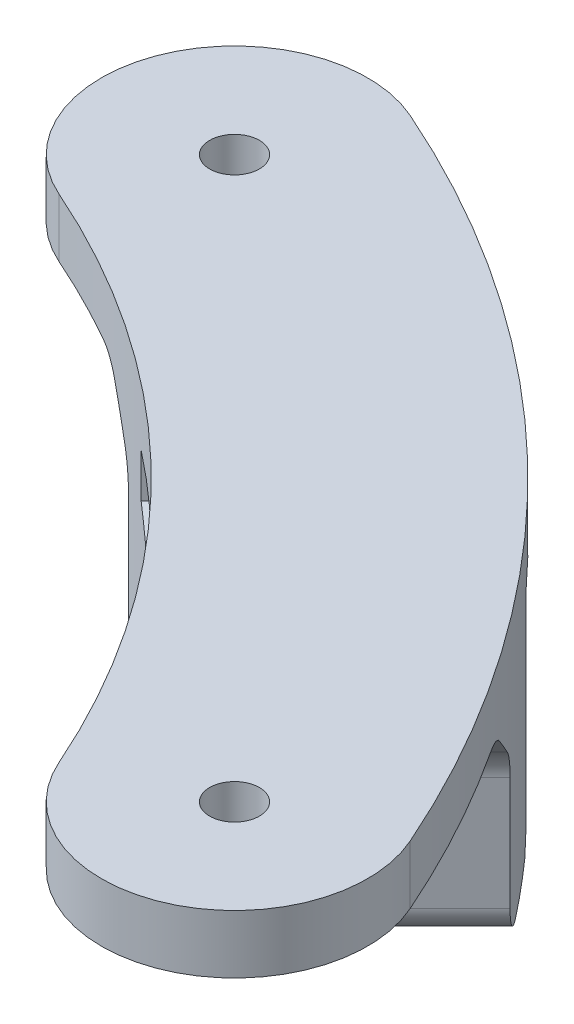
SolidWorks part; units mm, degrees
ref_plane "Front Plane" through (0, 0, 0) normal (0, 0, 1) x (1, 0, 0)
ref_plane "Top Plane" through (0, 0, 0) normal (0, 1, 0) x (1, 0, 0)
ref_plane "Right Plane" through (0, 0, 0) normal (1, 0, 0) x (0, 0, -1)
sketch "Sketch1" plane through (0, -74.9015, 0) normal (0, -1, 0) x (1, 0, 0)
  circle A0 centre (30.1717, -68.5087) radius 1.7
  circle A1 centre (68.5087, -30.1717) radius 1.7
  arc A2 (33.8428, -76.8444) -> (76.8444, -33.8428) centre (0, 0) ccw construction
  arc A3 (21.5669, -71.4952) -> (33.8428, -76.8444) centre (30.1717, -68.5087) ccw construction
  arc A4 (26.5006, -60.1729) -> (33.8428, -76.8444) centre (30.1717, -68.5087) ccw construction
  arc A5 (76.8444, -33.8428) -> (60.1729, -26.5006) centre (68.5087, -30.1717) ccw construction
  arc A6 (33.8428, -76.8444) -> (76.8444, -33.8428) centre (0, 0) ccw
  arc A7 (21.5669, -71.4952) -> (33.8428, -76.8444) centre (30.1717, -68.5087) ccw
  arc A8 (26.5006, -60.1729) -> (33.8428, -76.8444) centre (30.1717, -68.5087) ccw
  arc A9 (76.8444, -33.8428) -> (60.1729, -26.5006) centre (68.5087, -30.1717) ccw
  arc A10 (60.1729, -26.5006) -> (26.5006, -60.1729) centre (0, 0) cw
  arc M17 (21.5669, -71.4952) -> (33.8428, -76.8444) centre (30.1717, -68.5087) ccw
  arc M18 (33.8428, -76.8444) -> (76.8444, -33.8428) centre (0, 0) ccw
  arc M19 (76.8444, -33.8428) -> (71.4952, -21.5669) centre (68.5087, -30.1717) ccw
  circle M28 centre (68.5087, -30.1717) radius 1.7
  circle M29 centre (30.1717, -68.5087) radius 1.7
extrude "Boss-Extrude1" add sketch "Sketch1" along normal blind 4 contours A9 A10 A8 M17 M18 M19 M28 M29
ref_plane "Plane1" through (48.1381, 0, -48.1381) normal (0.7071, 0, -0.7071) x (-0.7071, 0, -0.7071)
ref_plane "Plane2" through (62.2802, 0, -62.2802) normal (0.7071, 0, -0.7071) x (-0.7071, 0, -0.7071)
sketch "Sketch2" plane through (62.2802, 0, -62.2802) normal (0.7071, 0, -0.7071) x (-0.7071, 0, -0.7071)
  line L0 (-12, -78.9015) -> (-12, -93.9015)
  line L1 (-30.4067, -78.9015) -> (30.4067, -78.9015) construction
  line L2 (-12, -93.9015) -> (-4, -93.9015)
  line L3 (-4, -93.9015) -> (-4, -78.9015)
  line L4 (-4, -78.9015) -> (-12, -78.9015)
  line L5 (0, -78.9015) -> (0, -94.9061) construction
  line L6 (4, -93.9015) -> (12, -93.9015)
  line L7 (12, -93.9015) -> (12, -78.9015)
  line L8 (12, -78.9015) -> (8, -78.9015)
  line L9 (8, -81.9015) -> (4, -84.2109)
  line L10 (4, -84.2109) -> (4, -93.9015)
  line L11 (8, -78.9015) -> (8, -81.9015)
  dimension "D1" = 8
  dimension "D2" = 15
  dimension "D3" = 8
  dimension "D4" = 3
  dimension "D5" = 120
  dimension "D6" = 4
extrude "Boss-Extrude2" add sketch "Sketch2" against normal blind 30
sketch "Sketch3" plane through (0, -93.9015, 0) normal (0, -1, 0) x (1, 0, 0)
  line L0 (29.4841, -58.7686) -> (22.0629, -51.3475)
  line L1 (22.0629, -51.3475) -> (52.6779, -23.0254)
  line L2 (52.6779, -23.0254) -> (58.6525, -29.7144)
  line L3 (72.7124, -41.9918) -> (86.4476, -52.4176)
  line L4 (86.4476, -52.4176) -> (48.4046, -83.5816)
  line L5 (48.4046, -83.5816) -> (40.7967, -73.3896)
  arc A0 (58.6525, -29.7144) -> (29.4841, -58.7686) centre (0, 0) cw
  circle A1 centre (0, 0) radius 65.75 construction
  arc A2 (72.7124, -41.9918) -> (40.7967, -73.3896) centre (0, 0) cw
  arc A3 (67.2492, -50.2787) -> (76.8444, -33.8428) centre (0, 0) ccw construction
  arc A4 (33.8428, -76.8444) -> (50.2787, -67.2492) centre (0, 0) ccw construction
extrude "Cut-Extrude1" cut sketch "Sketch3" against normal blind 30
sketch "Sketch4" plane through (8.4853, 0, 8.4853) normal (0.7071, 0, 0.7071) x (0.7071, 0, -0.7071)
  line L0 (64.6457, -93.9015) -> (83.1048, -93.9015) construction
  line L1 (65.6282, -78.9015) -> (65.6282, -93.9015) construction
  circle A0 centre (74.1282, -88.9015) radius 1.5
  dimension "D1" = 3
  dimension "D2" = 5
  dimension "D3" = 8.5
extrude "Cut-Extrude2" cut sketch "Sketch4" against normal through all
fillet "Fillet1" radius 2 2 edges at (43.7524, -93.9015, -60.7229) (60.7229, -93.9015, -43.7524)
chamfer "Chamfer1" distance 1 angle 45 2 edges at (55.6845, -93.9015, -50.0276) (50.0276, -93.9015, -55.6845)
chamfer "Chamfer2" distance 4 angle 45 2 edges at (43.7524, -78.9015, -60.7229) (60.7229, -78.9015, -43.7524)
fillet "Fillet2" radius 3 4 edges at (63.0038, -78.9015, -40.3764) (60.7229, -82.9015, -43.7524) (43.7524, -82.9015, -60.7229) (40.3764, -78.9015, -63.0038)
